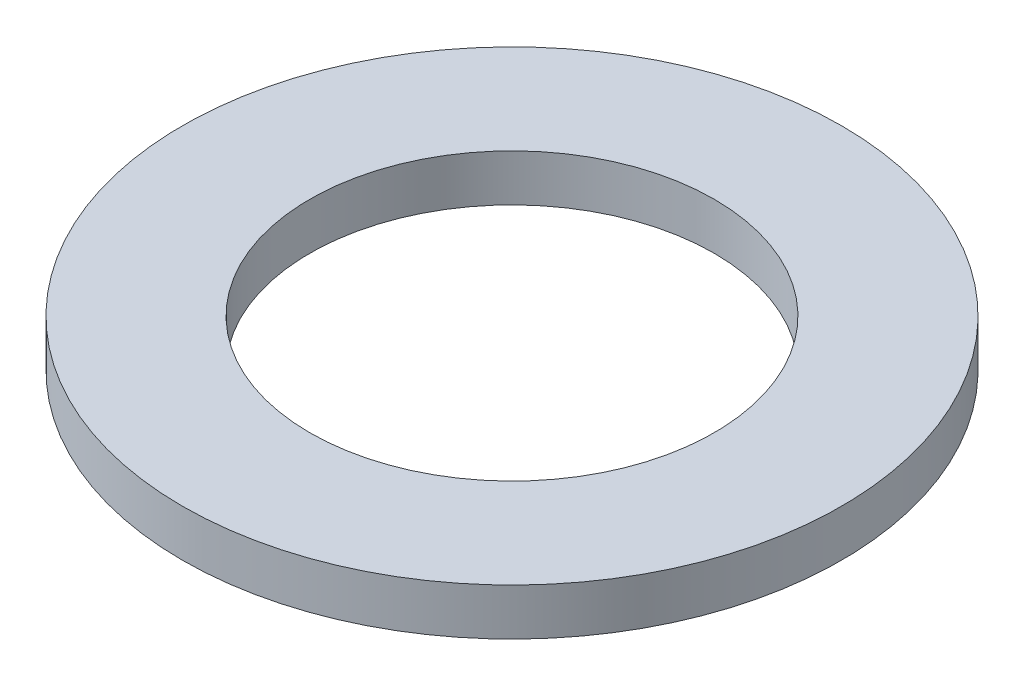
SolidWorks part; units mm, degrees
ref_plane "Front Plane" through (0, 0, 0) normal (0, 0, 1) x (1, 0, 0)
ref_plane "Top Plane" through (0, 0, 0) normal (0, 1, 0) x (1, 0, 0)
ref_plane "Right Plane" through (0, 0, 0) normal (1, 0, 0) x (0, 0, -1)
sketch "Sketch1" plane through (0, 0, 0) normal (0, 1, 0) x (1, 0, 0)
  circle A0 centre (0, 0) radius 3.429
  circle A1 centre (0, 0) radius 5.588
  dimension "D1" = 11.176
  dimension "D2" = 6.858
extrude "Boss-Extrude1" add sketch "Sketch1" along normal blind 0.7937
